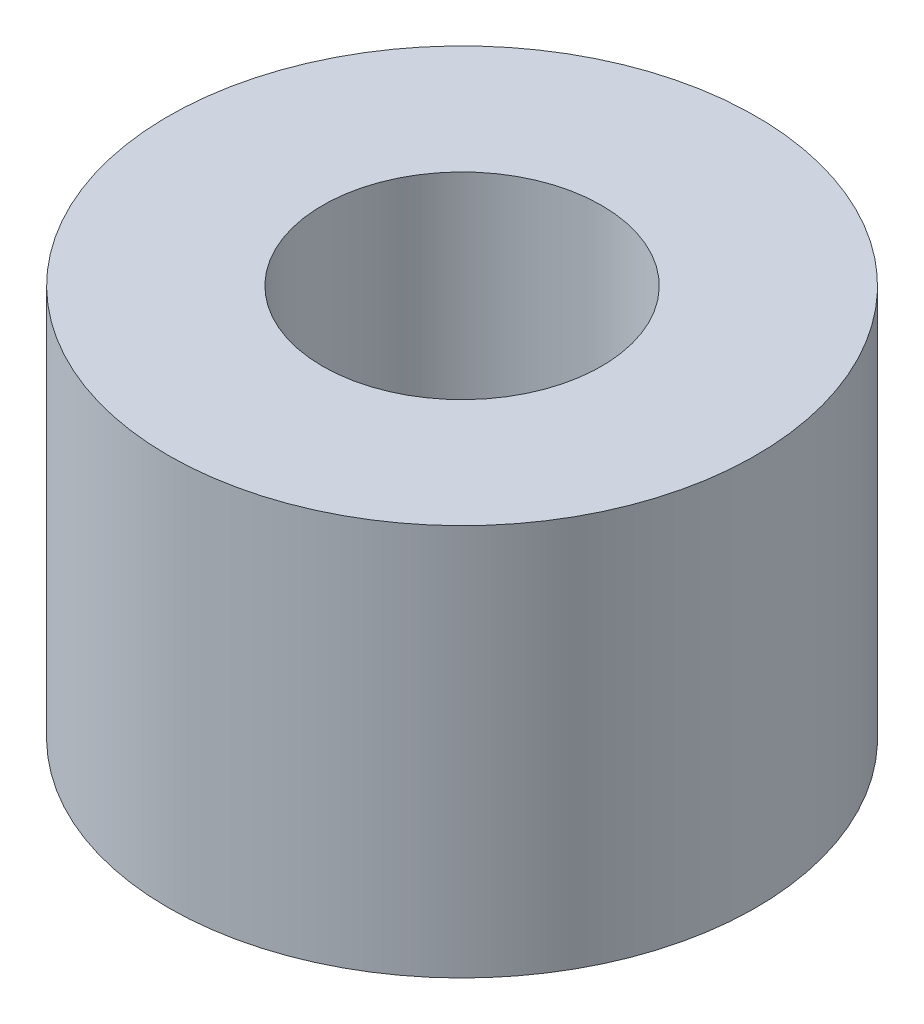
SolidWorks part; units mm, degrees
ref_plane "Front Plane" through (0, 0, 0) normal (0, 0, 1) x (1, 0, 0)
ref_plane "Top Plane" through (0, 0, 0) normal (0, 1, 0) x (1, 0, 0)
ref_plane "Right Plane" through (0, 0, 0) normal (1, 0, 0) x (0, 0, -1)
sketch "Sketch1" plane through (0, 0, 0) normal (0, 1, 0) x (1, 0, 0)
  circle A0 centre (0, 0) radius 2.3813
  dimension "D1" = 4.7625
extrude "Boss-Extrude1" add sketch "Sketch1" along normal blind 3.175
hole_wizard "Tap Drill for #4-40 Tap1" positions "Sketch3" profile "Sketch2" hole size "#4-40" standard "Ansi Inch"
sketch "Sketch3" plane through (0, 3.175, 0) normal (0, 1, 0) x (-1, 0, 0)
  circle A0 centre (0, 0) radius 2.3813 construction
  point P0 (0, 0)
sketch "Sketch2" plane through (0, 3.175, 0) normal (1, 0, 0) x (0, 0, 1)
  line L0 (0, 0) -> (0, 3.9812)
  line L1 (0, 3.9812) -> (1.1303, 3.302)
  line L2 (1.1303, 3.302) -> (1.1303, 0)
  line L5 (1.1303, 0) -> (0, 0)
  line L10 (0, 3.9812) -> (-1.1303, 3.302) construction
  line L11 (0, -6.35) -> (0, 107.95) construction
  dimension "Hole Dia." = 2.2606
  dimension "Hole Depth" = 3.302
  dimension "Drill Angle" = 118
